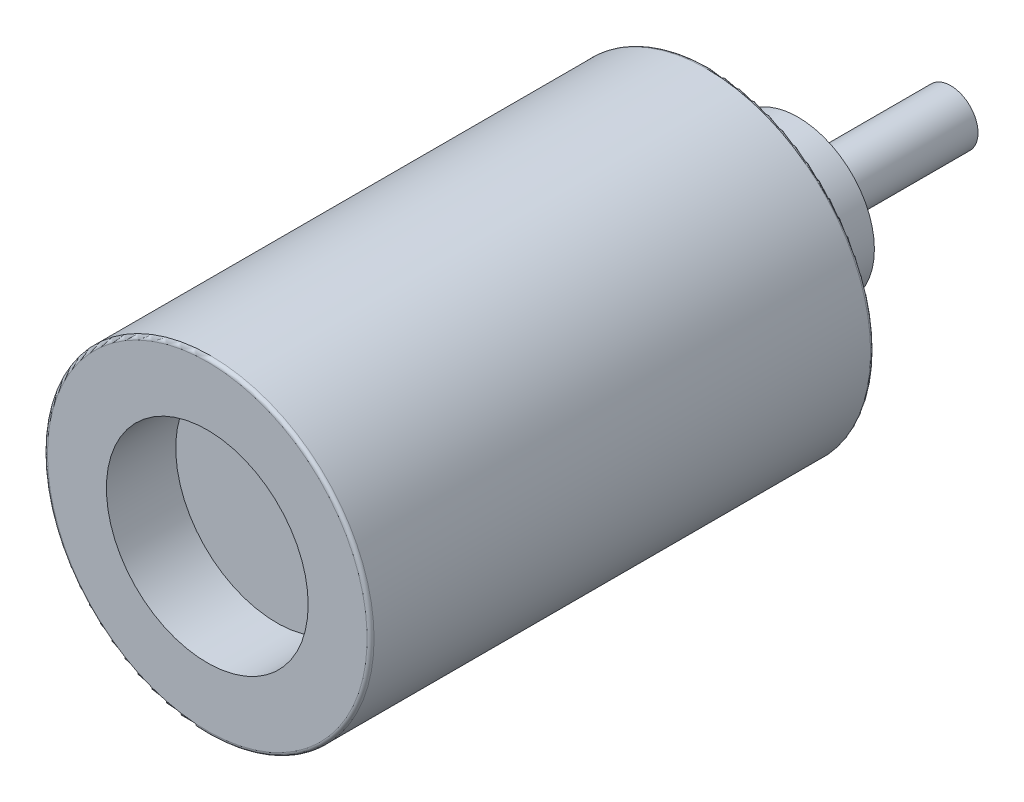
SolidWorks part; units mm, degrees
material "miniBoard"
ref_plane "Front Plane" through (0, 0, 0) normal (0, 0, 1) x (1, 0, 0)
ref_plane "Top Plane" through (0, 0, 0) normal (0, 1, 0) x (1, 0, 0)
ref_plane "Right Plane" through (0, 0, 0) normal (1, 0, 0) x (0, 0, -1)
sketch "Sketch1" plane through (0, 0, 0) normal (1, 0, 0) x (0, 0, -1)
  line L0 (-14.4044, 0) -> (94.0803, 0) construction
  line L1 (0, 2.9908) -> (9.2202, 2.9908)
  line L2 (0, 2.9908) -> (0, 1.8478)
  line L3 (0, 1.8478) -> (1.27, 1.8478)
  line L4 (1.27, 1.8478) -> (1.27, 0)
  line L5 (1.27, 0) -> (13.6144, 0)
  line L6 (9.2202, 2.9908) -> (9.2202, 1.397)
  line L7 (9.2202, 1.397) -> (10.8204, 1.397)
  line L8 (10.8204, 1.397) -> (10.8204, 0.5)
  line L9 (10.8204, 0.5) -> (13.6144, 0.5)
  line L10 (13.6144, 0.5) -> (13.6144, 0)
  dimension "D1" = 2.9908
  dimension "D2" = 1.143
  dimension "D3" = 1.27
  dimension "D4" = 1.6002
  dimension "D5" = 0.5
  dimension "D6" = 4.3942
  dimension "D7" = 9.2202
  dimension "D8" = 1.397
revolve "Revolve1" add sketch "Sketch1" angle 360 about L0
fillet "Fillet1" radius 0.0635 2 edges at (2.9908, 0, -9.2202) (2.9908, 0, 0)
